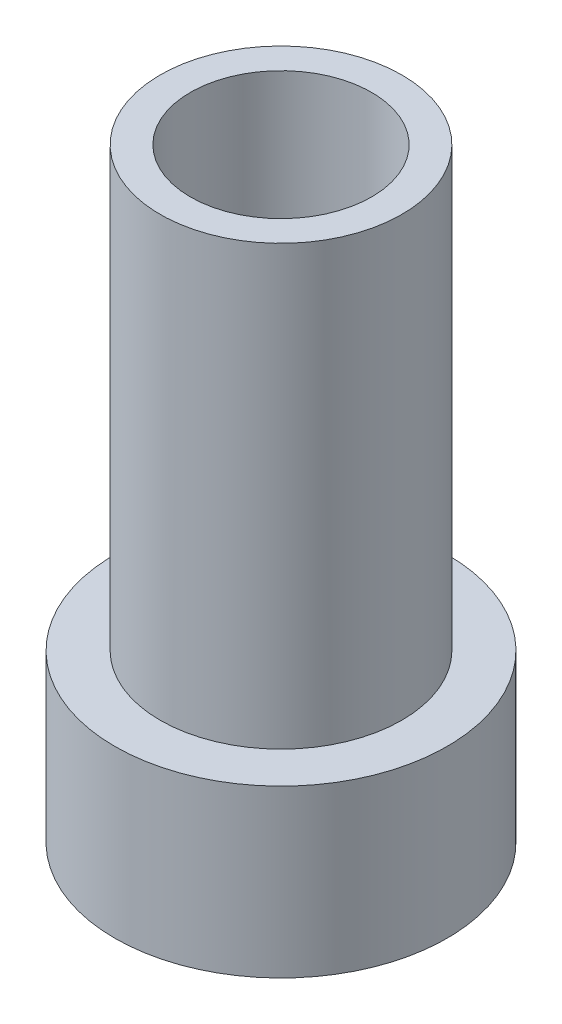
SolidWorks part; units mm, degrees
ref_plane "Спереди" through (0, 0, 0) normal (0, 0, 1) x (1, 0, 0)
ref_plane "Сверху" through (0, 0, 0) normal (0, 1, 0) x (1, 0, 0)
ref_plane "Справа" through (0, 0, 0) normal (1, 0, 0) x (0, 0, -1)
sketch "Эскиз1" plane through (0, 0, 0) normal (0, 0, 1) x (1, 0, 0)
  line L0 (0, 0) -> (0, 20) construction
  line L1 (4, 20) -> (4, 11)
  line L2 (4, 11) -> (5.5, 11)
  line L3 (5.5, 11) -> (5.5, 0)
  line L4 (5.5, 0) -> (0, 0)
  line L5 (4, 20) -> (0, 20)
  line L6 (0, 0) -> (0, 20)
  dimension "D1" = 11
  dimension "D2" = 11
  dimension "D3" = 8
  dimension "D4" = 1.5
  dimension "D5" = 20
revolve "Повернуть1" add sketch "Эскиз1" angle 360 about L0
sketch "Эскиз2" plane through (0, 20, 0) normal (0, 1, 0) x (1, 0, 0)
  circle A0 centre (0, 0) radius 3
  dimension "D1" = 6
extrude "Вырез-Вытянуть1" cut sketch "Эскиз2" against normal blind 10
sketch "Эскиз3" plane through (0, 0, 0) normal (0, -1, 0) x (1, 0, 0)
  circle A0 centre (0, 0) radius 2
  dimension "D1" = 4
extrude "Вырез-Вытянуть2" cut sketch "Эскиз3" against normal through all
sketch "Эскиз4" plane through (0, 11, 0) normal (0, 1, 0) x (1, 0, 0)
  circle A0 centre (0, 0) radius 4 construction
  circle A1 centre (0, 0) radius 5.5
  circle A2 centre (0, 0) radius 5.5
  circle A3 centre (0, 0) radius 4
  dimension "D1" = 0
extrude "Вырез-Вытянуть3" cut sketch "Эскиз4" against normal blind 5.5
